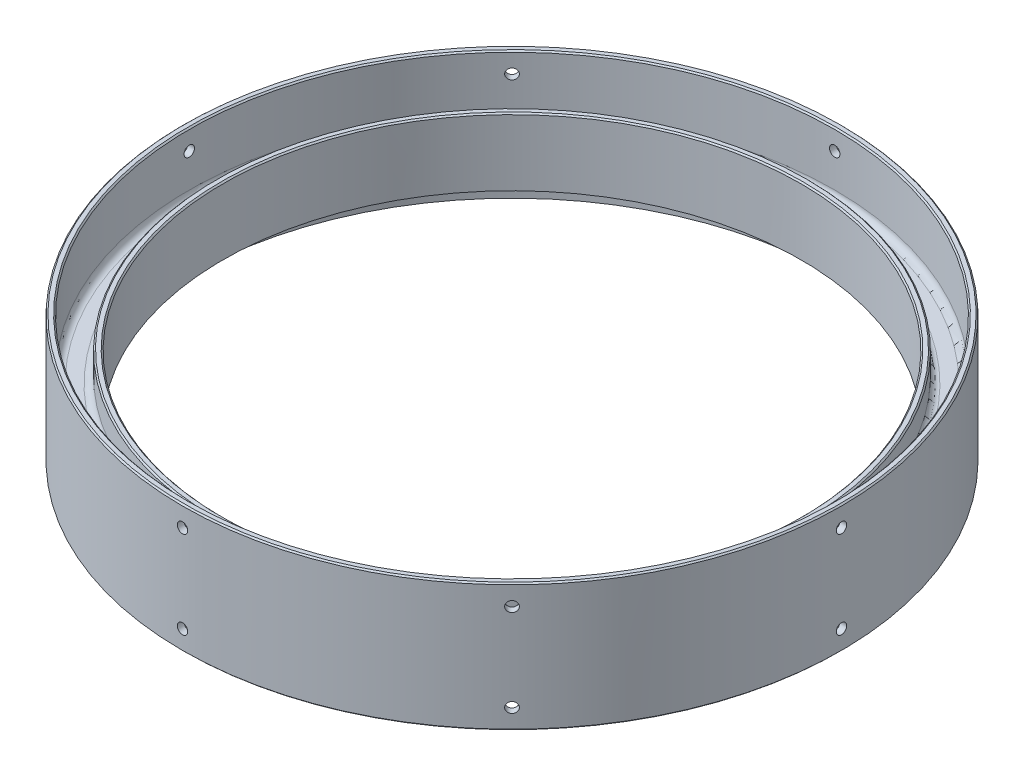
SolidWorks part; units mm, degrees
material "6061-T6 (SS)"
ref_plane "Front Plane" through (0, 0, 0) normal (0, 0, 1) x (1, 0, 0)
ref_plane "Top Plane" through (0, 0, 0) normal (0, 1, 0) x (1, 0, 0)
ref_plane "Right Plane" through (0, 0, 0) normal (1, 0, 0) x (0, 0, -1)
sketch "Sketch1" plane through (0, 0, 0) normal (0, 0, 1) x (1, 0, 0)
  line L0 (136.525, 15.875) -> (136.525, -15.875)
  line L1 (136.525, -15.875) -> (139.7, -15.875)
  line L2 (139.7, -15.875) -> (139.7, -1.5875)
  line L3 (139.7, -1.5875) -> (152.4, -1.5875)
  line L4 (152.4, -1.5875) -> (152.4, -30.1625)
  line L5 (152.4, -30.1625) -> (155.575, -30.1625)
  line L6 (155.575, -30.1625) -> (155.575, 30.1625)
  line L7 (155.575, 30.1625) -> (152.4, 30.1625)
  line L8 (152.4, 30.1625) -> (152.4, 1.5875)
  line L9 (152.4, 1.5875) -> (139.7, 1.5875)
  line L10 (139.7, 1.5875) -> (139.7, 15.875)
  line L11 (139.7, 15.875) -> (136.525, 15.875)
  line L12 (0, 0) -> (136.525, 0) construction
  line L13 (0, 44.4664) -> (0, -44.4664) construction
  point P17 (136.525, 0)
  dimension "D1" = 60.325
  dimension "D2" = 3.175
  dimension "D3" = 3.175
  dimension "D4" = 12.7
  dimension "D5" = 31.75
  dimension "D6" = 139.7
  dimension "D7" = 3.175
revolve "Revolve1" add sketch "Sketch1" angle 360 about L13
fillet "Fillet1" radius 3.175 4 edges at (0, -1.5875, 139.7) (0, -1.5875, 152.4) (0, 1.5875, 152.4) (0, 1.5875, 139.7)
sketch "Sketch3" plane through (0, 0, 0) normal (0, 1, 0) x (1, 0, 0)
  line L0 (88.9, 12.7) -> (88.9, -12.7)
  line L1 (88.9, -12.7) -> (135.1894, -19.05)
  line L2 (88.9, 12.7) -> (135.1894, 19.05)
  line L3 (0, 0) -> (88.9, 0) construction
  circle A0 centre (0, 0) radius 136.525 construction
  arc A1 (135.1894, -19.05) -> (135.1894, 19.05) centre (0, 0) ccw
  dimension "D1" = 88.9
  dimension "D2" = 25.4
  dimension "D3" = 38.1
ref_plane "Plane1" through (155.575, 0, 0) normal (1, 0, 0) x (0, 0, -1)
hole_wizard "#10 (0.1935) Diameter Hole1" positions "Sketch8" profile "Sketch9" hole size "#10" standard "ANSI Inch"
sketch "Sketch8" plane through (155.575, 0, 0) normal (1, 0, 0) x (0, 0, -1)
  line L0 (0, 20.6375) -> (0, -20.6375)
  point P0 (0, 20.6375)
  point P3 (0, -20.6375)
  point P9 (0, 0)
  dimension "D1" = 41.275
sketch "Sketch9" plane through (155.575, 20.6375, 0) normal (0, 1, 0) x (0, 0, -1)
  line L0 (0, 0) -> (0, 26.8766)
  line L1 (0, 26.8766) -> (2.4574, 25.4)
  line L2 (2.4574, 25.4) -> (2.4574, 0)
  line L5 (2.4574, 0) -> (0, 0)
  line L10 (0, 26.8766) -> (-2.4575, 25.4) construction
  line L11 (0, -6.35) -> (0, 107.95) construction
  dimension "Hole Dia." = 4.9149
  dimension "Hole Depth" = 25.4
  dimension "Drill Angle" = 118
pattern_circular "CirPattern7" count 8 over 360 about axis through (0, 30.1625, 0) along (0, 1, 0) of "#10 (0.1935) Diameter Hole1"
chamfer "Chamfer1" distance 0.635 angle 45 5 edges at (0, -30.1625, 155.575) (0, 30.1625, 155.575) (0, 30.1625, 152.4) (0, 15.875, 136.525) (0, 15.875, 139.7)
